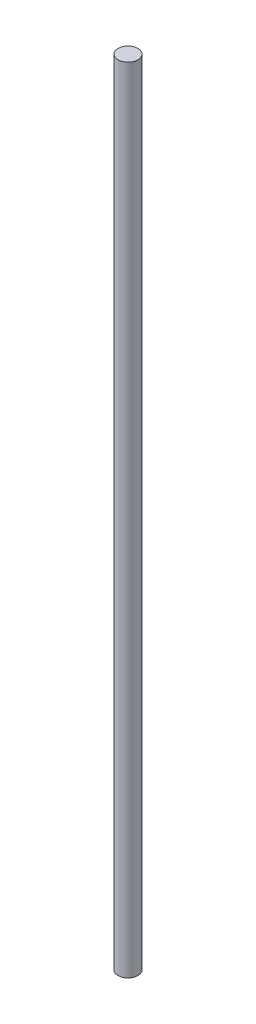
SolidWorks part; units mm, degrees
ref_plane "Front Plane" through (0, 0, 0) normal (0, 0, 1) x (1, 0, 0)
ref_plane "Top Plane" through (0, 0, 0) normal (0, 1, 0) x (1, 0, 0)
ref_plane "Right Plane" through (0, 0, 0) normal (1, 0, 0) x (0, 0, -1)
sketch "Sketch1" plane through (0, 0, 0) normal (0, 1, 0) x (1, 0, 0)
  circle A0 centre (0, 0) radius 5
  dimension "D1" = 10
extrude "Boss-Extrude1" add sketch "Sketch1" along normal blind 400
